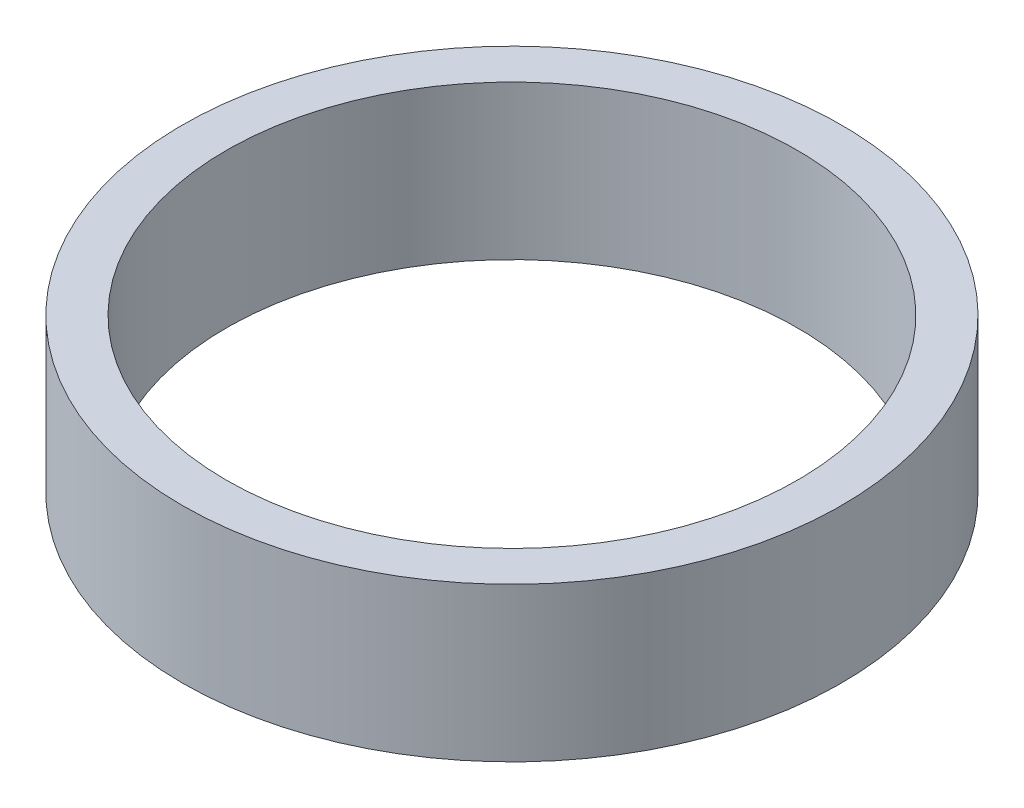
SolidWorks part; units mm, degrees
ref_plane "Front Plane" through (0, 0, 0) normal (0, 0, 1) x (1, 0, 0)
ref_plane "Top Plane" through (0, 0, 0) normal (0, 1, 0) x (1, 0, 0)
ref_plane "Right Plane" through (0, 0, 0) normal (1, 0, 0) x (0, 0, -1)
sketch "Sketch2" plane through (0, 0, 0) normal (0, 1, 0) x (1, 0, 0)
  circle A0 centre (0, 0) radius 6.5
  circle A1 centre (0, 0) radius 7.5
  dimension "D1" = 13
  dimension "D2" = 15
extrude "Boss-Extrude1" add sketch "Sketch2" along normal blind 3.5 contours A0 | A1
